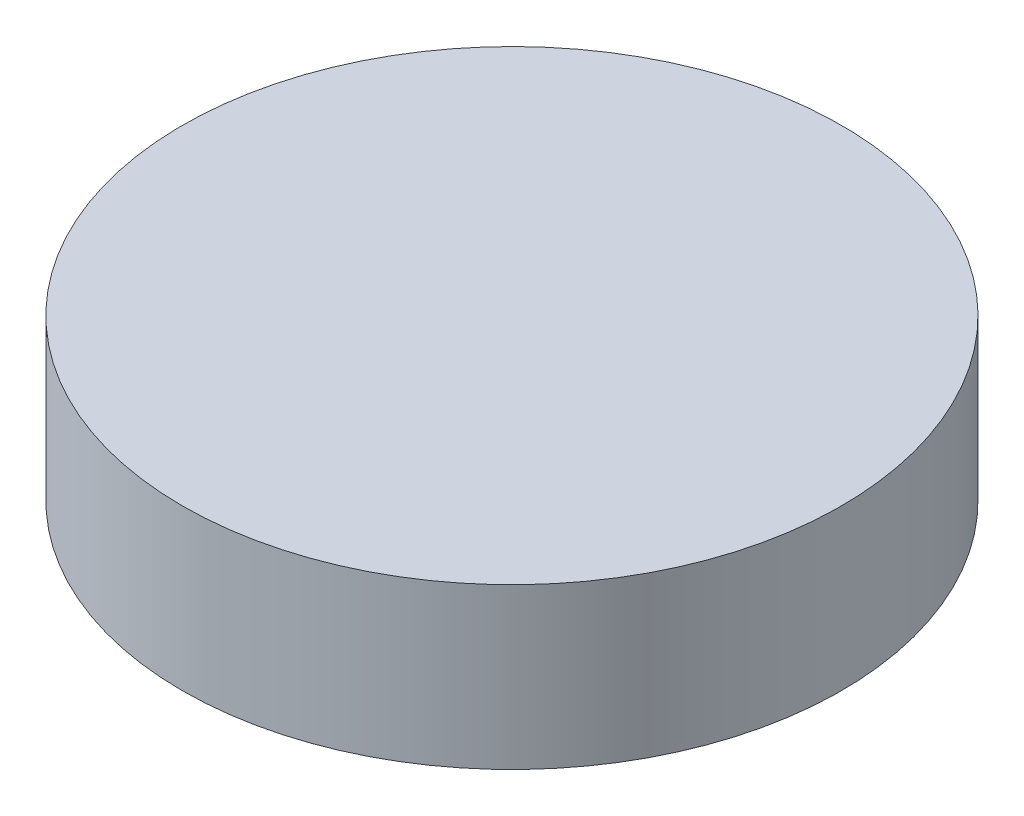
SolidWorks part; units mm, degrees
ref_plane "Front Plane" through (0, 0, 0) normal (0, 0, 1) x (1, 0, 0)
ref_plane "Top Plane" through (0, 0, 0) normal (0, 1, 0) x (1, 0, 0)
ref_plane "Right Plane" through (0, 0, 0) normal (1, 0, 0) x (0, 0, -1)
sketch "Sketch1" plane through (0, 0, 0) normal (0, 1, 0) x (1, 0, 0)
  circle A0 centre (0, 0) radius 20.59
  dimension "D1" = 41.18
extrude "Boss-Extrude1" add sketch "Sketch1" along normal blind 10
